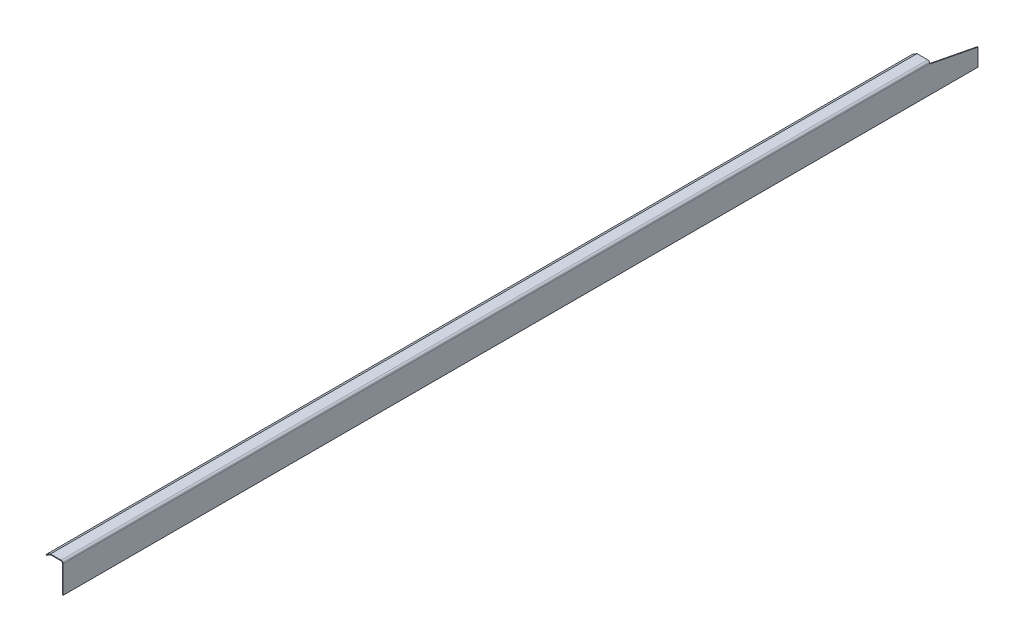
SolidWorks part; units mm, degrees
ref_plane "Front Plane" through (0, 0, 0) normal (0, 0, 1) x (1, 0, 0)
ref_plane "Top Plane" through (0, 0, 0) normal (0, 1, 0) x (1, 0, 0)
ref_plane "Right Plane" through (0, 0, 0) normal (1, 0, 0) x (0, 0, -1)
sketch "Sketch1" plane through (0, 0, 0) normal (0, 0, 1) x (1, 0, 0)
  line L0 (1143, 0) -> (1142.2062, 0)
  line L1 (1143, 32.5437) -> (1143, 0)
  line L2 (1142.2062, 0) -> (1142.2062, 32.5437)
  line L3 (1127.9187, 34.925) -> (1140.6188, 34.925)
  line L4 (1140.6188, 34.1313) -> (1128.1405, 34.1313)
  line L5 (1123.0914, 31.0712) -> (1128.1405, 34.1313)
  line L6 (1122.68, 31.75) -> (1123.0914, 31.0712)
  line L7 (1127.9187, 34.925) -> (1122.68, 31.75)
  arc A0 (1143, 32.5437) -> (1140.6188, 34.925) centre (1140.6188, 32.5437) ccw
  arc A1 (1142.2062, 32.5437) -> (1140.6188, 34.1313) centre (1140.6188, 32.5437) ccw
extrude "Extrude1" add sketch "Sketch1" along normal mid plane 1084.2625
sketch "Sketch2" plane through (1143, 0, 0) normal (1, 0, 0) x (0, 0, -1)
  line L0 (542.1312, 0) -> (542.1312, 20.6502) construction
  line L1 (542.1312, 0) -> (542.1312, 32.5437) construction
  line L2 (542.1312, 34.925) -> (484.9812, 34.925)
  line L3 (-542.1312, 34.925) -> (542.1312, 34.925) construction
  line L4 (484.9812, 34.925) -> (484.9812, 31.75)
  line L5 (484.9812, 31.75) -> (542.1312, 20.6502)
  line L6 (542.1312, 20.6502) -> (542.1312, 34.925)
extrude "Cut-Extrude1" cut sketch "Sketch2" against normal blind 25.4
sketch "Sketch3" plane through (0, 0, -484.9812) normal (0, 0, -1) x (-1, 0, 0)
  line L0 (-1127.9187, 34.925) -> (-1122.68, 31.75)
  line L1 (-1122.68, 31.75) -> (-1123.4204, 30.5283)
  line L2 (-1123.4204, 30.5283) -> (-1128.1405, 34.1313)
  line L3 (-1128.1405, 34.1313) -> (-1127.9187, 34.925)
extrude "Cut-Extrude2" cut sketch "Sketch3" along normal blind 25.4
